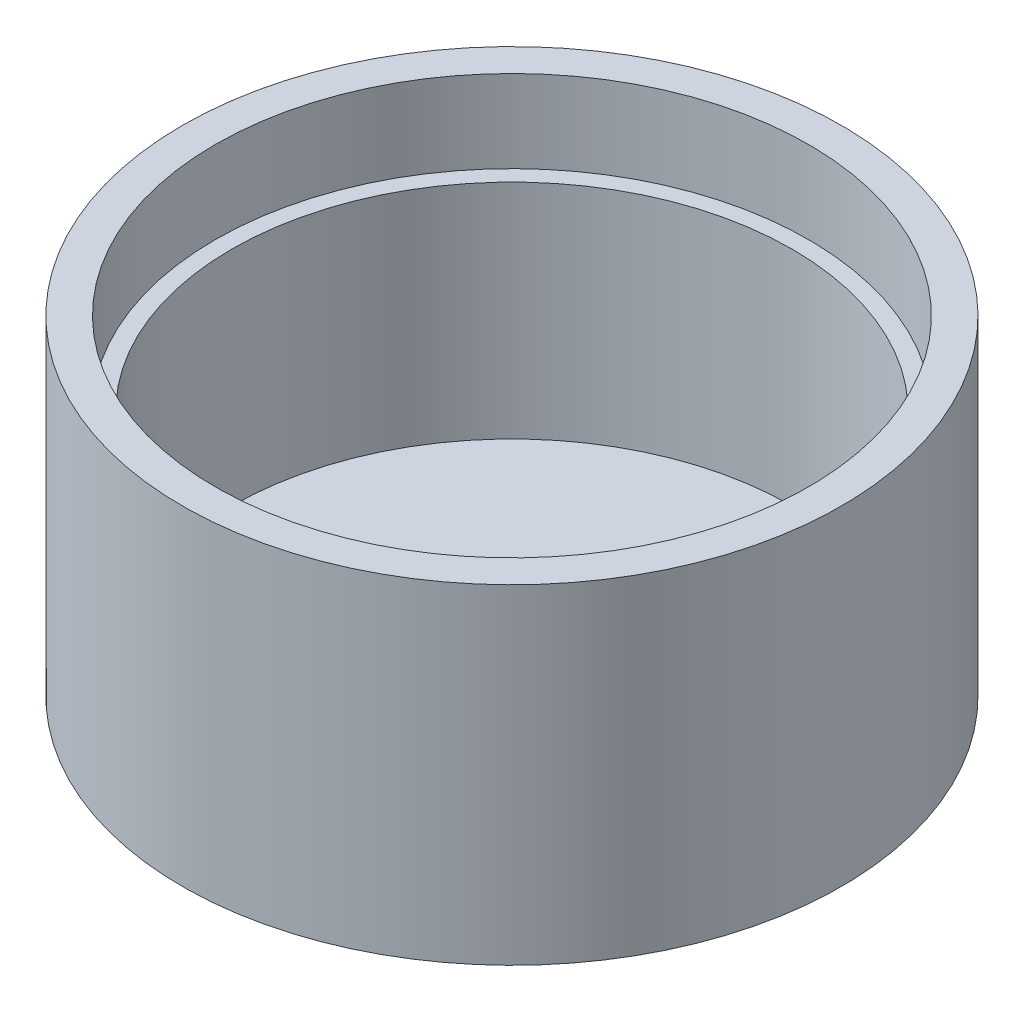
SolidWorks part; units mm, degrees
ref_plane "Front Plane" through (0, 0, 0) normal (0, 0, 1) x (1, 0, 0)
ref_plane "Top Plane" through (0, 0, 0) normal (0, 1, 0) x (1, 0, 0)
ref_plane "Right Plane" through (0, 0, 0) normal (1, 0, 0) x (0, 0, -1)
sketch "Sketch1" plane through (0, 0, 0) normal (0, 0, 1) x (1, 0, 0)
  line L6 (0, 0) -> (20, 0)
  line L7 (20, 0) -> (20, 20)
  line L8 (20, 20) -> (18, 20)
  line L9 (18, 20) -> (18, 15)
  line L10 (18, 15) -> (17, 15)
  line L11 (17, 15) -> (17, 1.5)
  line L12 (17, 1.5) -> (0, 1.5)
  line L13 (0, 1.5) -> (0, 0)
  dimension "D1" = 20
  dimension "D2" = 5
  dimension "D3" = 2
  dimension "D4" = 1
  dimension "D5" = 1.5
  dimension "D6" = 20
revolve "Revolve1" add sketch "Sketch1" angle 360 about L13
